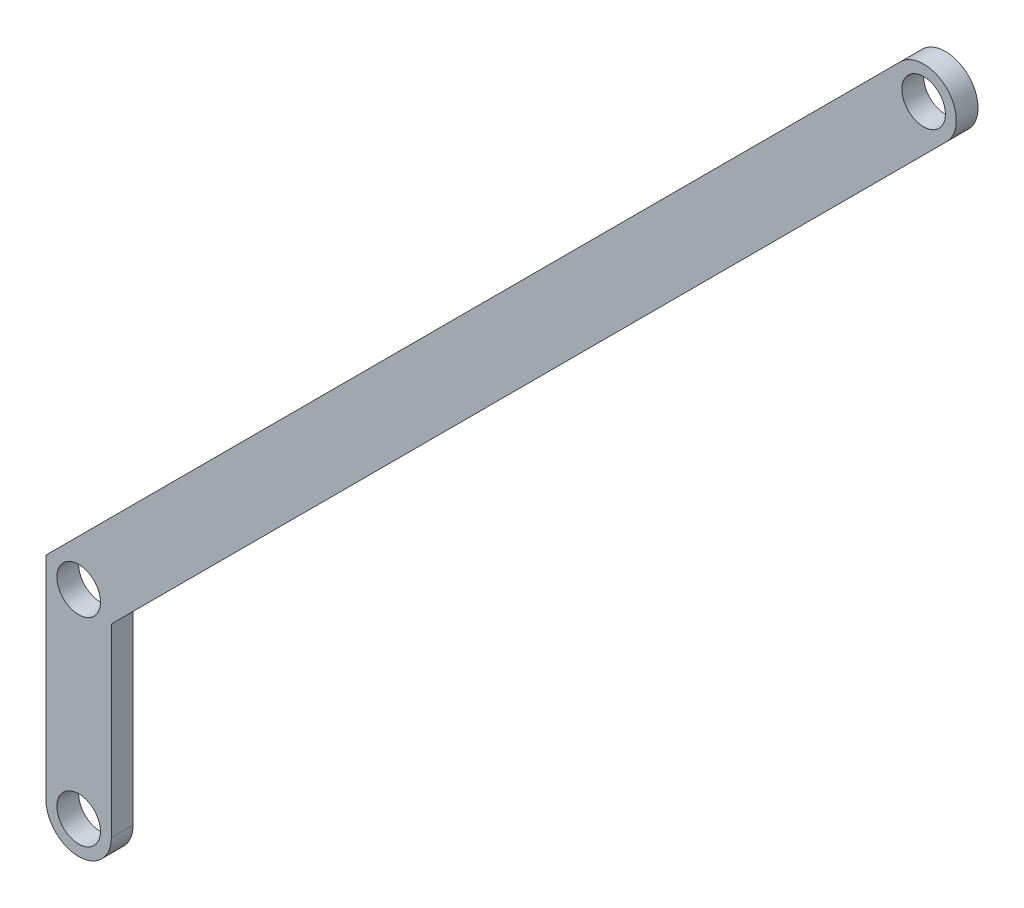
SolidWorks part; units mm, degrees
ref_plane "Front Plane" through (0, 0, 0) normal (0, 0, 1) x (1, 0, 0)
ref_plane "Top Plane" through (0, 0, 0) normal (0, 1, 0) x (1, 0, 0)
ref_plane "Right Plane" through (0, 0, 0) normal (1, 0, 0) x (0, 0, -1)
other "Center of Mass"
sketch "Sketch1" plane through (0, 0, 0) normal (0, 0, 1) x (1, 0, 0)
  line L0 (-97.7711, 14.822) -> (-97.7711, -41.3912)
  line L1 (-97.7711, 14.822) -> (103.7543, 216.3475)
  line L2 (-97.7711, -41.3912) -> (-82.7711, -41.3912)
  line L3 (-82.7711, -41.3912) -> (-82.7711, 8.6088)
  line L4 (-82.7711, 8.6088) -> (114.3609, 205.7409)
  line L5 (114.3609, 205.7409) -> (103.7543, 216.3475)
  dimension "D1" = 15
  dimension "D2" = 15
  dimension "D3" = 50
  dimension "D4" = 56.2132
  dimension "D5" = 285
extrude "Boss-Extrude1" add sketch "Sketch1" along normal blind 5
sketch "Sketch2" plane through (0, 0, 5) normal (0, 0, 1) x (1, 0, 0)
  line L0 (-90.2711, -41.3912) -> (-90.2711, 34.2348) construction
  line L1 (-97.7711, -41.3912) -> (-82.7711, -41.3912) construction
  line L2 (109.0576, 211.0442) -> (-104.2421, -2.2555) construction
  line L3 (114.3609, 205.7409) -> (103.7543, 216.3475) construction
  line L10 (103.7543, 216.3475) -> (-97.7711, 14.822)
  line L11 (-97.7711, 14.822) -> (-97.7711, -41.3912)
  line L12 (-97.7711, -41.3912) -> (-82.7711, -41.3912)
  line L13 (-82.7711, -41.3912) -> (-82.7711, 8.6088)
  line L14 (-82.7711, 8.6088) -> (114.3609, 205.7409)
  line L15 (114.3609, 205.7409) -> (103.7543, 216.3475)
  line L16 (103.7543, 216.3475) -> (-97.7711, 14.822)
  line L17 (-97.7711, 14.822) -> (-97.7711, -41.3912)
  line L18 (-97.7711, -41.3912) -> (-82.7711, -41.3912)
  line L19 (-82.7711, -41.3912) -> (-82.7711, 8.6088)
  line L20 (-82.7711, 8.6088) -> (114.3609, 205.7409)
  line L21 (114.3609, 205.7409) -> (103.7543, 216.3475)
  circle A0 centre (103.7543, 205.7409) radius 7.5
  circle A1 centre (-90.2711, -33.8912) radius 7.5
  circle A2 centre (103.7543, 205.7409) radius 5
  circle A3 centre (-90.2711, -33.8912) radius 5
  line M8 (103.7543, 216.3475) -> (-97.7711, 14.822)
  line M10 (-97.7711, -41.3912) -> (-82.7711, -41.3912)
  line M11 (-82.7711, -41.3912) -> (-82.7711, 8.6088)
  line M13 (114.3609, 205.7409) -> (103.7543, 216.3475)
  dimension "D3" = 0
  dimension "D4" = 15
  dimension "D1" = 7.5
  dimension "D2" = 7.5
extrude "Cut-Extrude1" cut sketch "Sketch2" against normal blind 5 contours A3 | A1 L17 M10 | A1 L18 M11 | A2 | A0 L21 M8 | A0 L20 M13
sketch "Sketch3" plane through (0, 0, 5) normal (0, 0, 1) x (1, 0, 0)
  line L0 (-97.7711, 14.822) -> (-82.7711, 8.6088) construction
  circle A0 centre (-90.2711, 11.7154) radius 5
extrude "Cut-Extrude2" cut sketch "Sketch3" against normal through all
